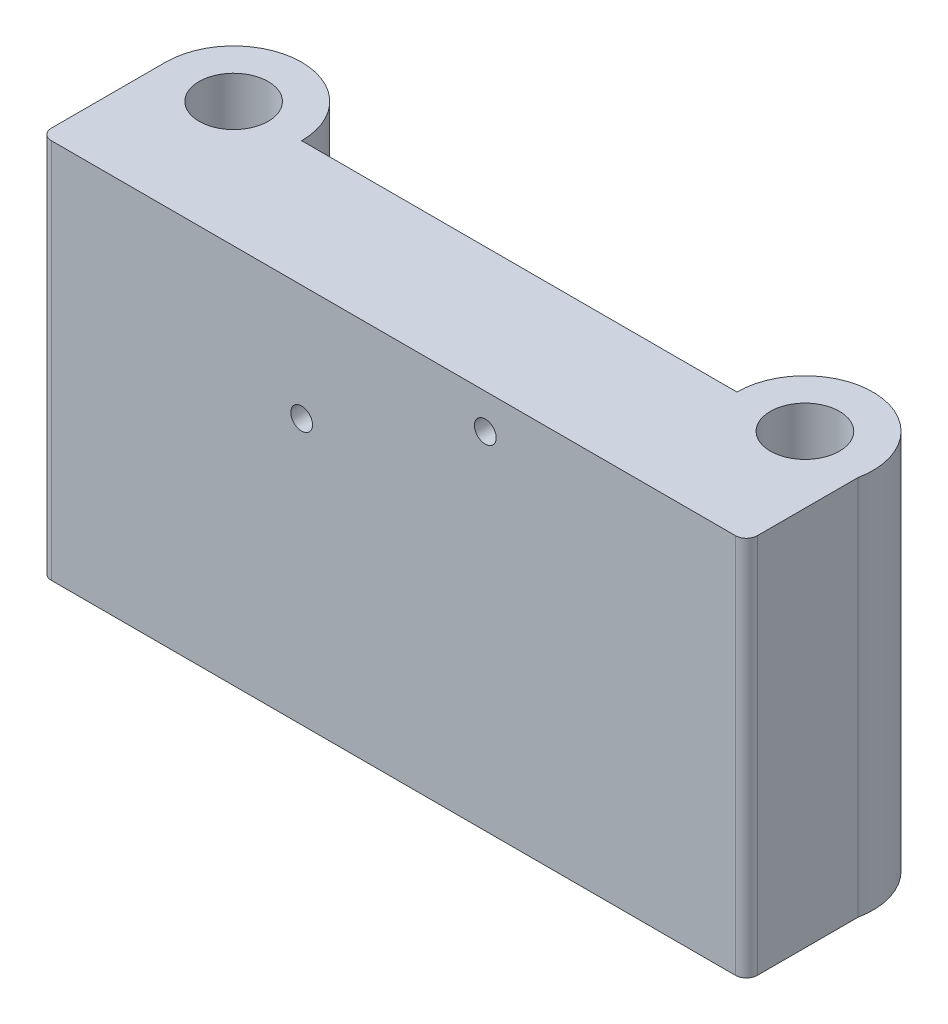
SolidWorks part; units mm, degrees
ref_plane "Front Plane" through (0, 0, 0) normal (0, 0, 1) x (1, 0, 0)
ref_plane "Top Plane" through (0, 0, 0) normal (0, 1, 0) x (1, 0, 0)
ref_plane "Right Plane" through (0, 0, 0) normal (1, 0, 0) x (0, 0, -1)
sketch "Sketch1" plane through (0, 0, 0) normal (0, 1, 0) x (1, 0, 0)
  line L1 (-24.9858, 0) -> (15.0205, 0)
  line L2 (-37.4858, 0) -> (-37.4858, -11.5)
  line L3 (-37.4858, -11.5) -> (27.3942, -11.5)
  line L4 (27.3942, -1.25) -> (27.3942, -11.5)
  arc A0 (-24.9858, 0) -> (-37.4858, 0) centre (-31.2358, 0) ccw
  arc A1 (27.3942, -1.25) -> (15.0205, 0) centre (21.2705, 0) ccw
  point P4 (0, 0)
  dimension "D1" = 12.5
  dimension "D2" = 12.5
  dimension "D3" = 11.5
  dimension "D4" = 64.88
extrude "Boss-Extrude1" add sketch "Sketch1" along normal blind 35
sketch "Sketch2" plane through (0, 35, 0) normal (0, 1, 0) x (1, 0, 0)
  circle A0 centre (-31.2358, 0) radius 3.175
  circle A1 centre (21.2705, 0) radius 3.175
  dimension "D1" = 6.35
  dimension "D2" = 6.35
extrude "Cut-Extrude1" cut sketch "Sketch2" against normal through all
sketch "Sketch3" plane through (0, 0, 0) normal (0, -1, 0) x (1, 0, 0)
  circle A0 centre (21.2705, 0) radius 4.25
  circle A1 centre (-31.2358, 0) radius 4.25
  dimension "D1" = 8.5
  dimension "D2" = 8.5
extrude "Cut-Extrude2" cut sketch "Sketch3" against normal blind 9
sketch "Sketch4" plane through (0, 0, 11.5) normal (0, 0, 1) x (1, 0, 0)
  line L0 (-37.4858, 35) -> (-37.4858, 0) construction
  line L1 (27.3942, 35) -> (27.3942, 0) construction
  line L2 (-37.4858, 35) -> (27.3942, 35) construction
  circle A0 centre (-13.4858, 24.385) radius 1
  circle A1 centre (3.3942, 31.785) radius 1
  dimension "D1" = 2
  dimension "D2" = 2
  dimension "D5" = 3.215
  dimension "D3" = 24
  dimension "D4" = 24
  dimension "D6" = 10.615
extrude "Cut-Extrude4" cut sketch "Sketch4" against normal through all
fillet "Fillet1" radius 1 2 edges at (27.3942, 17.5, 11.5) (-37.4858, 17.5, 11.5)
